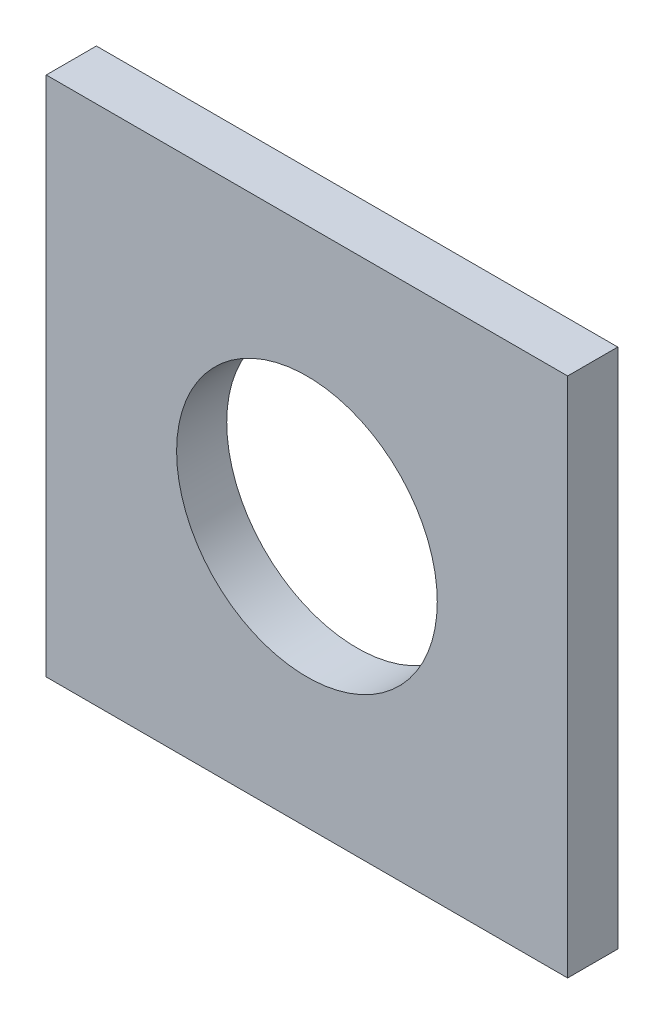
SolidWorks part; units mm, degrees
material "Plain Carbon Steel"
ref_plane "Front Plane" through (0, 0, 0) normal (0, 0, 1) x (1, 0, 0)
ref_plane "Top Plane" through (0, 0, 0) normal (0, 1, 0) x (1, 0, 0)
ref_plane "Right Plane" through (0, 0, 0) normal (1, 0, 0) x (0, 0, -1)
sketch "Sketch1" plane through (0, 0, 0) normal (0, 0, 1) x (1, 0, 0)
  line L1 (-41.275, -41.275) -> (41.275, -41.275)
  line L2 (-41.275, -41.275) -> (-41.275, 41.275)
  line L3 (-41.275, 41.275) -> (41.275, 41.275)
  line L4 (41.275, -41.275) -> (41.275, 41.275)
  line L5 (-41.275, -41.275) -> (41.275, 41.275) construction
  line L6 (-41.275, 41.275) -> (41.275, -41.275) construction
  circle A0 centre (0, 0) radius 20.6375
  dimension "D1" = 41.275
  dimension "D2" = 82.55
extrude "Boss-Extrude1" add sketch "Sketch1" along normal blind 7.9375
